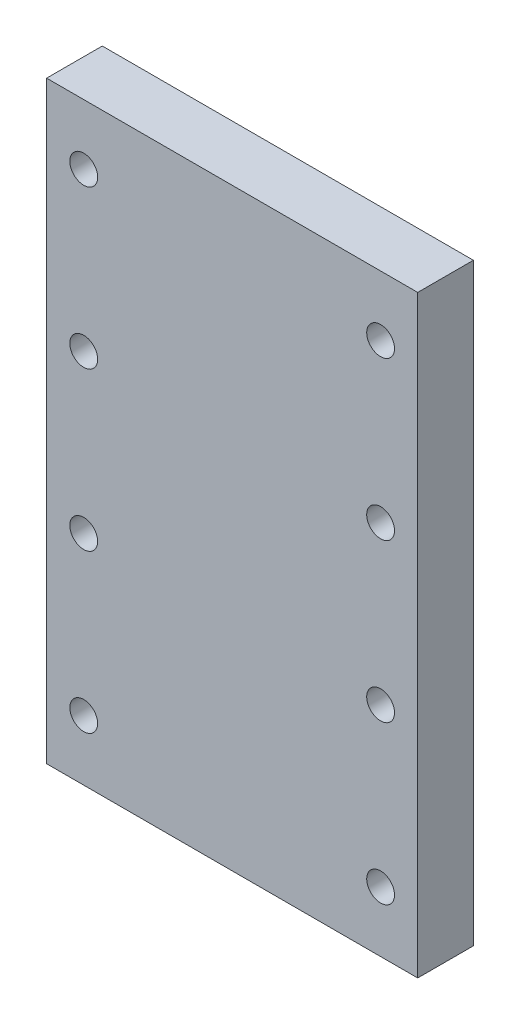
SolidWorks part; units mm, degrees
material "6061 Alloy"
ref_plane "Front Plane" through (0, 0, 0) normal (0, 0, 1) x (1, 0, 0)
ref_plane "Top Plane" through (0, 0, 0) normal (0, 1, 0) x (1, 0, 0)
ref_plane "Right Plane" through (0, 0, 0) normal (1, 0, 0) x (0, 0, -1)
sketch "Sketch1" plane through (0, 0, 0) normal (0, 0, 1) x (1, 0, 0)
  line L1 (-32.8889, 3.5556) -> (7.1111, 3.5556)
  line L2 (-32.8889, 3.5556) -> (-32.8889, 67.5556)
  line L3 (-32.8889, 67.5556) -> (7.1111, 67.5556)
  line L4 (7.1111, 3.5556) -> (7.1111, 67.5556)
  dimension "D1" = 40
  dimension "D2" = 64
extrude "Boss-Extrude1" add sketch "Sketch1" along normal blind 6
sketch "Sketch2" plane through (0, 0, 6) normal (0, 0, 1) x (1, 0, 0)
  line L0 (-28.8889, 61.0556) -> (-28.8889, 10.0556)
  line L1 (3.1111, 61.0556) -> (3.1111, 10.0556)
  line L2 (-32.8889, 67.5556) -> (-32.8889, 3.5556) construction
  line L3 (7.1111, 67.5556) -> (-32.8889, 67.5556) construction
  circle A0 centre (-28.8889, 61.0556) radius 1.5
  circle A1 centre (3.1111, 61.0556) radius 1.5
  circle A2 centre (3.1111, 44.0556) radius 1.5
  circle A3 centre (3.1111, 27.0556) radius 1.5
  circle A4 centre (3.1111, 10.0556) radius 1.5
  circle A5 centre (-28.8889, 10.0556) radius 1.5
  circle A6 centre (-28.8889, 27.0556) radius 1.5
  circle A7 centre (-28.8889, 44.0556) radius 1.5
  point P20 (0, 0)
  point P21 (0, 0)
  point P22 (3.5235, 42.1445)
  point P23 (0, 0)
  dimension "D3" = 6.5
  dimension "D1" = 4
  dimension "D2" = 32
  dimension "D4" = 6.5
  dimension "D5" = 17
  dimension "D6" = 17
  dimension "D7" = 17
  dimension "D8" = 17
  dimension "D9" = 17
  dimension "D10" = 17
extrude "Cut-Extrude1" cut sketch "Sketch2" against normal through all both and the other way through all
